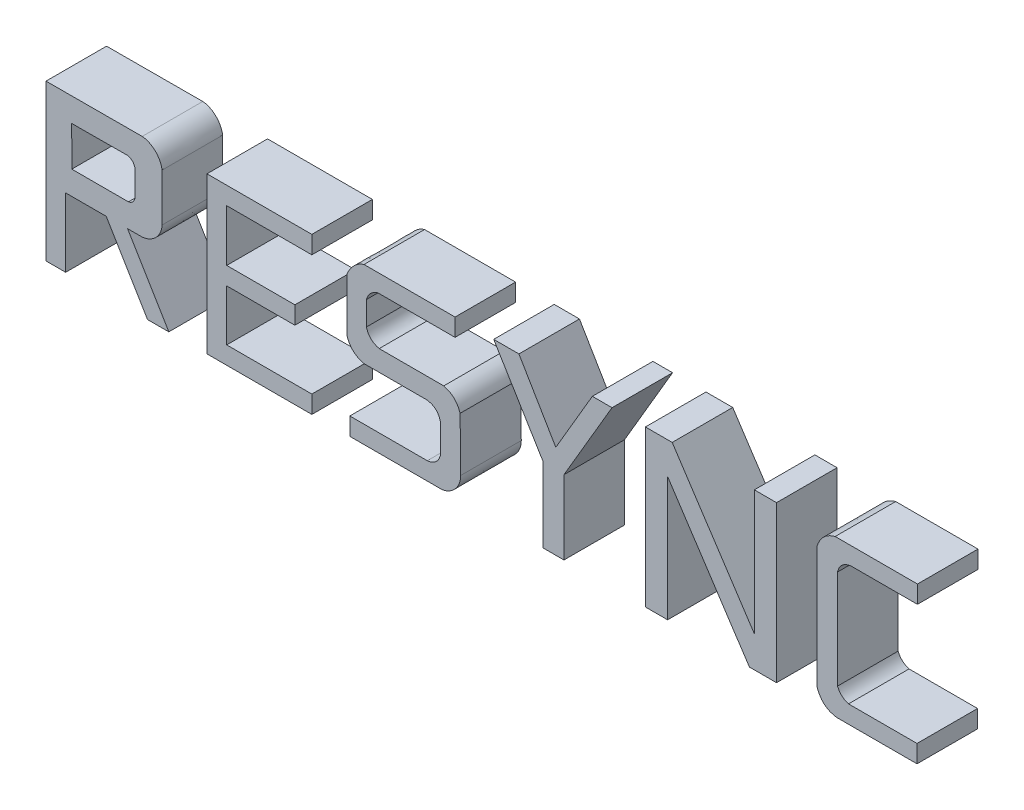
SolidWorks part; units mm, degrees
ref_plane "Front Plane" through (0, 0, 0) normal (0, 0, 1) x (1, 0, 0)
ref_plane "Top Plane" through (0, 0, 0) normal (0, 1, 0) x (1, 0, 0)
ref_plane "Right Plane" through (0, 0, 0) normal (1, 0, 0) x (0, 0, -1)
sketch "Sketch39" plane through (0, 0, 0) normal (0, 0, 1) x (1, 0, 0)
  line L0 (147.6667, 279.75) -> (830.3333, 279.75) construction
  line L1 (297, 531.75) -> (1577, 531.75) construction
  line L2 (-15.0225, 6.9502) -> (-15.0225, 1.4057)
  line L3 (-15.0225, 1.4057) -> (-13.9728, 1.4057)
  line L4 (-13.9728, 1.4057) -> (-13.9728, 3.6779)
  line L5 (-13.9728, 3.6779) -> (-12.9478, 3.6779)
  line L6 (-12.9478, 3.6779) -> (-11.5831, 1.4057)
  line L7 (-11.5831, 1.4057) -> (-10.4121, 1.4057)
  line L8 (-10.4121, 1.4057) -> (-11.7768, 3.6779)
  line L9 (-11.7768, 3.6779) -> (-11.6385, 3.6779)
  line L10 (-10.7883, 4.5476) -> (-10.7883, 6.1322)
  line L11 (-11.6385, 6.9576) -> (-15.0225, 6.9502)
  line L12 (-13.9728, 5.9647) -> (-13.9699, 4.6587)
  line L13 (-13.9699, 4.6587) -> (-12.0989, 4.6587)
  line L14 (-11.885, 4.8692) -> (-11.885, 5.7351)
  line L15 (-12.1205, 5.972) -> (-13.9728, 5.9647)
  line L16 (-9.7048, 6.9576) -> (-9.7048, 1.4057)
  line L17 (-9.7048, 1.4057) -> (-5.8401, 1.4057)
  line L18 (-5.8401, 1.4057) -> (-5.8401, 2.3891)
  line L19 (-5.8401, 2.3891) -> (-8.6526, 2.3891)
  line L20 (-8.6526, 2.3891) -> (-8.6526, 3.6779)
  line L21 (-8.6526, 3.6779) -> (-6.4009, 3.6779)
  line L22 (-6.4009, 3.6779) -> (-6.4009, 4.6624)
  line L23 (-6.4009, 4.6624) -> (-8.6526, 4.6624)
  line L24 (-8.6526, 4.6624) -> (-8.6526, 5.972)
  line L25 (-8.6526, 5.972) -> (-5.8401, 5.972)
  line L26 (-5.8401, 5.972) -> (-5.8401, 6.9576)
  line L27 (-5.8401, 6.9576) -> (-9.7048, 6.9576)
  line L28 (-4.9866, 1.4057) -> (-1.7436, 1.4057)
  line L29 (-0.9222, 2.3209) -> (-0.9432, 4.116)
  line L30 (-1.6562, 4.8018) -> (-3.7908, 4.8018)
  line L31 (-4.0366, 5.0385) -> (-4.0366, 5.7632)
  line L32 (-3.8276, 5.976) -> (-1.1096, 5.976)
  line L33 (-1.1096, 5.976) -> (-1.1096, 6.9576)
  line L34 (-1.1096, 6.9576) -> (-4.3432, 6.9576)
  line L35 (-5.0828, 6.2212) -> (-5.0828, 4.4143)
  line L36 (-4.3432, 3.7217) -> (-2.2708, 3.7217)
  line L37 (-1.9972, 3.5013) -> (-1.9972, 2.5759)
  line L38 (-2.2357, 2.3891) -> (-4.9866, 2.3891)
  line L39 (-4.9866, 2.3891) -> (-4.9866, 1.4057)
  line L40 (-0.3891, 6.9576) -> (1.3981, 4.0225)
  line L41 (1.3981, 4.0225) -> (1.3981, 1.4057)
  line L42 (1.3981, 1.4057) -> (2.4881, 1.4057)
  line L43 (2.4881, 1.4057) -> (2.4881, 3.9919)
  line L44 (2.4881, 3.9919) -> (4.2251, 6.9576)
  line L45 (4.2251, 6.9576) -> (3.1117, 6.9576)
  line L46 (3.1117, 6.9576) -> (2.0173, 5.0892)
  line L47 (2.0173, 5.0892) -> (0.9145, 6.9576)
  line L48 (0.9145, 6.9576) -> (-0.3891, 6.9576)
  line L49 (4.7787, 6.9576) -> (4.7787, 1.4057)
  line L50 (4.7787, 1.4057) -> (5.9124, 1.4057)
  line L51 (5.9124, 1.4057) -> (5.9124, 5.0385)
  line L52 (5.9124, 5.0385) -> (8.3065, 1.4057)
  line L53 (8.3065, 1.4057) -> (9.5107, 1.4057)
  line L54 (9.5107, 1.4057) -> (9.5107, 6.9576)
  line L55 (9.5107, 6.9576) -> (8.377, 6.9576)
  line L56 (8.377, 6.9576) -> (8.377, 3.307)
  line L57 (8.377, 3.307) -> (5.971, 6.9576)
  line L58 (5.971, 6.9576) -> (4.7787, 6.9576)
  line L59 (11.2204, 6.9576) -> (14.1659, 6.9576)
  line L60 (14.1659, 6.9576) -> (14.1659, 5.976)
  line L61 (14.1659, 5.976) -> (11.8028, 5.976)
  line L62 (11.525, 5.7538) -> (11.525, 2.5629)
  line L63 (11.7216, 2.3891) -> (14.1513, 2.3891)
  line L64 (14.1513, 2.3891) -> (14.1513, 1.4057)
  line L65 (14.1513, 1.4057) -> (11.2756, 1.4057)
  line L66 (10.4471, 2.1356) -> (10.4471, 6.2043)
  line L128 (-11.6441, 6.7576) -> (-14.8225, 6.7506)
  line L129 (-14.8225, 6.7506) -> (-14.8225, 1.6057)
  line L130 (-14.8225, 1.6057) -> (-14.1728, 1.6057)
  line L131 (-14.1728, 1.6057) -> (-14.1728, 3.8779)
  line L132 (-14.1728, 3.8779) -> (-12.8347, 3.8779)
  line L133 (-12.8347, 3.8779) -> (-11.4699, 1.6057)
  line L134 (-11.4699, 1.6057) -> (-10.7655, 1.6057)
  line L135 (-10.7655, 1.6057) -> (-12.1302, 3.8779)
  line L136 (-12.1302, 3.8779) -> (-11.6459, 3.8779)
  line L137 (-10.9883, 4.551) -> (-10.9883, 6.1214)
  line L138 (-6.0401, 6.7576) -> (-9.5048, 6.7576)
  line L139 (-9.5048, 6.7576) -> (-9.5048, 1.6057)
  line L140 (-9.5048, 1.6057) -> (-6.0401, 1.6057)
  line L141 (-6.0401, 1.6057) -> (-6.0401, 2.1891)
  line L142 (-6.0401, 2.1891) -> (-8.8526, 2.1891)
  line L143 (-8.8526, 2.1891) -> (-8.8526, 3.8779)
  line L144 (-8.8526, 3.8779) -> (-6.6009, 3.8779)
  line L145 (-6.6009, 3.8779) -> (-6.6009, 4.4624)
  line L146 (-6.6009, 4.4624) -> (-8.8526, 4.4624)
  line L147 (-8.8526, 4.4624) -> (-8.8526, 6.172)
  line L148 (-8.8526, 6.172) -> (-6.0401, 6.172)
  line L149 (-6.0401, 6.172) -> (-6.0401, 6.7576)
  line L150 (-1.7972, 3.5273) -> (-1.7972, 2.5433)
  line L151 (-2.2268, 2.1891) -> (-4.7866, 2.1891)
  line L152 (-4.7866, 2.1891) -> (-4.7866, 1.6057)
  line L153 (-4.7866, 1.6057) -> (-1.7522, 1.6057)
  line L154 (-1.1222, 2.3186) -> (-1.1429, 4.0854)
  line L155 (-1.6825, 4.6018) -> (-3.8161, 4.6018)
  line L156 (-4.2366, 5.01) -> (-4.2366, 5.7953)
  line L157 (-3.8624, 6.176) -> (-1.3096, 6.176)
  line L158 (-1.3096, 6.176) -> (-1.3096, 6.7576)
  line L159 (-1.3096, 6.7576) -> (-4.3174, 6.7576)
  line L160 (-4.8828, 6.1875) -> (-4.8828, 4.4455)
  line L161 (-4.3192, 3.9217) -> (-2.2641, 3.9217)
  line L162 (0.8003, 6.7576) -> (-0.0332, 6.7576)
  line L163 (-0.0332, 6.7576) -> (1.5981, 4.0786)
  line L164 (1.5981, 4.0786) -> (1.5981, 1.6057)
  line L165 (1.5981, 1.6057) -> (2.2881, 1.6057)
  line L166 (2.2881, 1.6057) -> (2.2881, 4.0462)
  line L167 (2.2881, 4.0462) -> (3.8762, 6.7576)
  line L168 (3.8762, 6.7576) -> (3.2263, 6.7576)
  line L169 (3.2263, 6.7576) -> (2.018, 4.6946)
  line L170 (2.018, 4.6946) -> (0.8003, 6.7576)
  line L171 (5.8633, 6.7576) -> (4.9787, 6.7576)
  line L172 (4.9787, 6.7576) -> (4.9787, 1.6057)
  line L173 (4.9787, 1.6057) -> (5.7124, 1.6057)
  line L174 (5.7124, 1.6057) -> (5.7124, 5.7054)
  line L175 (5.7124, 5.7054) -> (8.4143, 1.6057)
  line L176 (8.4143, 1.6057) -> (9.3107, 1.6057)
  line L177 (9.3107, 1.6057) -> (9.3107, 6.7576)
  line L178 (9.3107, 6.7576) -> (8.577, 6.7576)
  line L179 (8.577, 6.7576) -> (8.577, 2.64)
  line L180 (8.577, 2.64) -> (5.8633, 6.7576)
  line L181 (11.2466, 6.7576) -> (13.9659, 6.7576)
  line L182 (13.9659, 6.7576) -> (13.9659, 6.176)
  line L183 (13.9659, 6.176) -> (11.7966, 6.176)
  line L184 (11.325, 5.7809) -> (11.325, 2.5157)
  line L185 (11.6877, 2.1891) -> (13.9513, 2.1891)
  line L186 (13.9513, 2.1891) -> (13.9513, 1.6057)
  line L187 (13.9513, 1.6057) -> (11.2905, 1.6057)
  line L188 (10.6471, 2.1662) -> (10.6471, 6.1755)
  spline S0 degree 3 poles (-11.6385, 3.6779) (-11.1992, 3.7086) (-10.8033, 4.0794) (-10.7883, 4.5476) knots 0 0 0 0 1 1 1 1
  spline S1 degree 3 poles (-10.7883, 6.1322) (-10.8311, 6.5559) (-11.2076, 6.9342) (-11.6385, 6.9576) knots 0 0 0 0 1 1 1 1
  spline S2 degree 2 poles (-12.0989, 4.6587) (-11.9219, 4.6939) (-11.885, 4.8692) knots 0 0 0 1 1 1
  spline S3 degree 2 poles (-11.885, 5.7351) (-11.9286, 5.9229) (-12.1205, 5.972) knots 0 0 0 1 1 1
  spline S4 degree 3 poles (-1.7436, 1.4057) (-1.3804, 1.4351) (-0.9949, 1.7823) (-0.9211, 2.2256) (-0.9222, 2.3209) knots 0 0 0 0 0.786572 1 1 1 1
  spline S5 degree 2 poles (-0.9432, 4.116) (-1.0994, 4.659) (-1.6562, 4.8018) knots 0 0 0 1 1 1
  spline S6 degree 2 poles (-3.7908, 4.8018) (-3.9821, 4.8512) (-4.0366, 5.0385) knots 0 0 0 1 1 1
  spline S7 degree 2 poles (-4.0366, 5.7632) (-3.9851, 5.9195) (-3.8276, 5.976) knots 0 0 0 1 1 1
  spline S8 degree 3 poles (-4.3432, 6.9576) (-4.7111, 6.8668) (-4.9695, 6.562) (-5.0828, 6.2212) knots 0 0 0 0 1 1 1 1
  spline S9 degree 2 poles (-5.0828, 4.4143) (-4.911, 3.8544) (-4.3432, 3.7217) knots 0 0 0 1 1 1
  spline S10 degree 2 poles (-2.2708, 3.7217) (-2.0516, 3.7069) (-1.9972, 3.5013) knots 0 0 0 1 1 1
  spline S11 degree 2 poles (-1.9972, 2.5759) (-2.0542, 2.4054) (-2.2357, 2.3891) knots 0 0 0 1 1 1
  spline S12 degree 2 poles (11.8028, 5.976) (11.5825, 5.9623) (11.525, 5.7538) knots 0 0 0 1 1 1
  spline S13 degree 2 poles (11.525, 2.5629) (11.5888, 2.4355) (11.7216, 2.3891) knots 0 0 0 1 1 1
  spline S14 degree 2 poles (11.2756, 1.4057) (10.6391, 1.4971) (10.4471, 2.1356) knots 0 0 0 1 1 1
  spline S15 degree 2 poles (10.4471, 6.2043) (10.6161, 6.8025) (11.2204, 6.9576) knots 0 0 0 1 1 1
  spline S16 degree 1 poles (-11.6459, 3.8779) (-10.9883, 4.551) knots 0 0 1 1 construction
  spline S17 degree 1 poles (-10.9883, 6.1214) (-11.6441, 6.7576) knots 0 0 1 1 construction
  spline S18 degree 3 poles (-11.6459, 3.8779) (-11.4798, 3.8912) (-11.1509, 4.0463) (-10.9944, 4.3834) (-10.9883, 4.551) knots 0.00646 0.00646 0.00646 0.00646 0.501839 0.997218 0.997218 0.997218 0.997218
  spline S19 degree 3 poles (-10.9883, 6.1214) (-11.007, 6.2822) (-11.1733, 6.5927) (-11.4844, 6.7475) (-11.6441, 6.7576) knots 0.009746 0.009746 0.009746 0.009746 0.50215 0.994555 0.994555 0.994555 0.994555
  spline S20 degree 1 poles (-1.7972, 2.5433) (-2.2268, 2.1891) knots 0 0 1 1 construction
  spline S21 degree 1 poles (-1.7522, 1.6057) (-1.1222, 2.3186) knots 0 0 1 1 construction
  spline S22 degree 1 poles (-1.1429, 4.0854) (-1.6825, 4.6018) knots 0 0 1 1 construction
  spline S23 degree 1 poles (-3.8161, 4.6018) (-4.2366, 5.01) knots 0 0 1 1 construction
  spline S24 degree 1 poles (-4.2366, 5.7953) (-3.8624, 6.176) knots 0 0 1 1 construction
  spline S25 degree 1 poles (-4.3174, 6.7576) (-4.8828, 6.1875) knots 0 0 1 1 construction
  spline S26 degree 1 poles (-4.8828, 4.4455) (-4.3192, 3.9217) knots 0 0 1 1 construction
  spline S27 degree 1 poles (-2.2641, 3.9217) (-1.7972, 3.5273) knots 0 0 1 1 construction
  spline S28 degree 3 poles (-1.7972, 2.5433) (-1.8034, 2.5246) (-1.8133, 2.4916) (-1.8589, 2.3917) (-1.9749, 2.2501) (-2.1273, 2.198) (-2.2268, 2.1891) knots -0.090605 -0.090605 -0.090605 -0.090605 0.048789 0.188183 0.466971 1.024547 1.024547 1.024547 1.024547
  spline S29 degree 3 poles (-1.7522, 1.6057) (-1.584, 1.6214) (-1.2586, 1.8045) (-1.1203, 2.1493) (-1.1222, 2.3186) knots 0.007182 0.007182 0.007182 0.007182 0.503591 1 1 1 1
  spline S30 degree 3 poles (-1.1429, 4.0854) (-1.1633, 4.1504) (-1.221, 4.2821) (-1.3336, 4.4205) (-1.4779, 4.5286) (-1.6153, 4.583) (-1.6825, 4.6018) knots 0.027378 0.027378 0.027378 0.027378 0.264292 0.501205 0.738119 0.975033 0.975033 0.975033 0.975033
  spline S31 degree 3 poles (-3.8161, 4.6018) (-3.9152, 4.6274) (-4.0598, 4.6889) (-4.1939, 4.8726) (-4.2229, 4.9629) (-4.2366, 5.01) knots -0.064176 -0.064176 -0.064176 -0.064176 0.504399 0.788687 1.072975 1.072975 1.072975 1.072975
  spline S32 degree 3 poles (-4.2366, 5.7953) (-4.2306, 5.8136) (-4.2209, 5.8461) (-4.178, 5.9429) (-4.1069, 6.0395) (-3.9811, 6.1334) (-3.9034, 6.1613) (-3.8624, 6.176) knots -0.097478 -0.097478 -0.097478 -0.097478 0.052698 0.202873 0.503224 0.803575 1.103927 1.103927 1.103927 1.103927
  spline S33 degree 3 poles (-4.3174, 6.7576) (-4.575, 6.6852) (-4.7912, 6.439) (-4.8828, 6.1875) knots 0.025806 0.025806 0.025806 0.025806 0.965955 0.965955 0.965955 0.965955
  spline S34 degree 3 poles (-4.8828, 4.4455) (-4.8602, 4.3782) (-4.7975, 4.2414) (-4.6785, 4.0999) (-4.5287, 3.9916) (-4.388, 3.9392) (-4.3192, 3.9217) knots 0.029157 0.029157 0.029157 0.029157 0.266245 0.503332 0.74042 0.977507 0.977507 0.977507 0.977507
  spline S35 degree 3 poles (-2.2641, 3.9217) (-2.1546, 3.9143) (-1.9864, 3.8635) (-1.8395, 3.673) (-1.8104, 3.5773) (-1.7972, 3.5273) knots -0.015332 -0.015332 -0.015332 -0.015332 0.522922 0.792048 1.061175 1.061175 1.061175 1.061175
  spline S36 degree 1 poles (10.6471, 6.1755) (11.2466, 6.7576) knots 0 0 1 1 construction
  spline S37 degree 1 poles (11.7966, 6.176) (11.325, 5.7809) knots 0 0 1 1 construction
  spline S38 degree 1 poles (11.325, 2.5157) (11.6877, 2.1891) knots 0 0 1 1 construction
  spline S39 degree 1 poles (11.2905, 1.6057) (10.6471, 2.1662) knots 0 0 1 1 construction
  spline S40 degree 3 poles (10.6471, 6.1755) (10.6696, 6.2489) (10.7336, 6.3981) (10.8594, 6.555) (11.0202, 6.6766) (11.1722, 6.7369) (11.2466, 6.7576) knots 0.025179 0.025179 0.025179 0.025179 0.263179 0.501179 0.73918 0.97718 0.97718 0.97718 0.97718
  spline S41 degree 3 poles (11.7966, 6.176) (11.6864, 6.1692) (11.5168, 6.1177) (11.3689, 5.9271) (11.3389, 5.831) (11.325, 5.7809) knots -0.014073 -0.014073 -0.014073 -0.014073 0.524245 0.793404 1.062562 1.062562 1.062562 1.062562
  spline S42 degree 3 poles (11.325, 2.5157) (11.3419, 2.482) (11.3702, 2.4196) (11.4643, 2.3059) (11.5535, 2.2432) (11.6441, 2.2033) (11.6717, 2.1947) (11.6877, 2.1891) knots -0.165845 -0.165845 -0.165845 -0.165845 0.155777 0.477398 0.79902 0.959831 1.120641 1.120641 1.120641 1.120641
  spline S43 degree 3 poles (11.2905, 1.6057) (11.2123, 1.6179) (11.0496, 1.6632) (10.8808, 1.7733) (10.7453, 1.9271) (10.6725, 2.0879) (10.6471, 2.1662) knots 0.012558 0.012558 0.012558 0.012558 0.253225 0.493892 0.734559 0.975225 0.975225 0.975225 0.975225
  dimension "D1" = 0.2
  dimension "D2" = 0.2
extrude "Boss-Extrude1" add sketch "Sketch39" along normal blind 2 contours L137 S19 L128 L129 L130 L131 L132 L133 L134 L135 L136 S18 S3 L14 S2 L13 L12 L15 | L148 L149 L138 L139 L140 L141 L142 L143 L144 L145 L146 L147 | L161 S35 L150 S28 L151 L152 L153 S29 L154 S30 L155 S31 L156 S32 L157 L158 L159 S33 L160 S34 | L169 L170 L162 L163 L164 L165 L166 L167 L168 | L179 L180 L171 L172 L173 L174 L175 L176 L177 L178 | L184 S42 L185 L186 L187 S43 L188 S40 L181 L182 L183 S41
